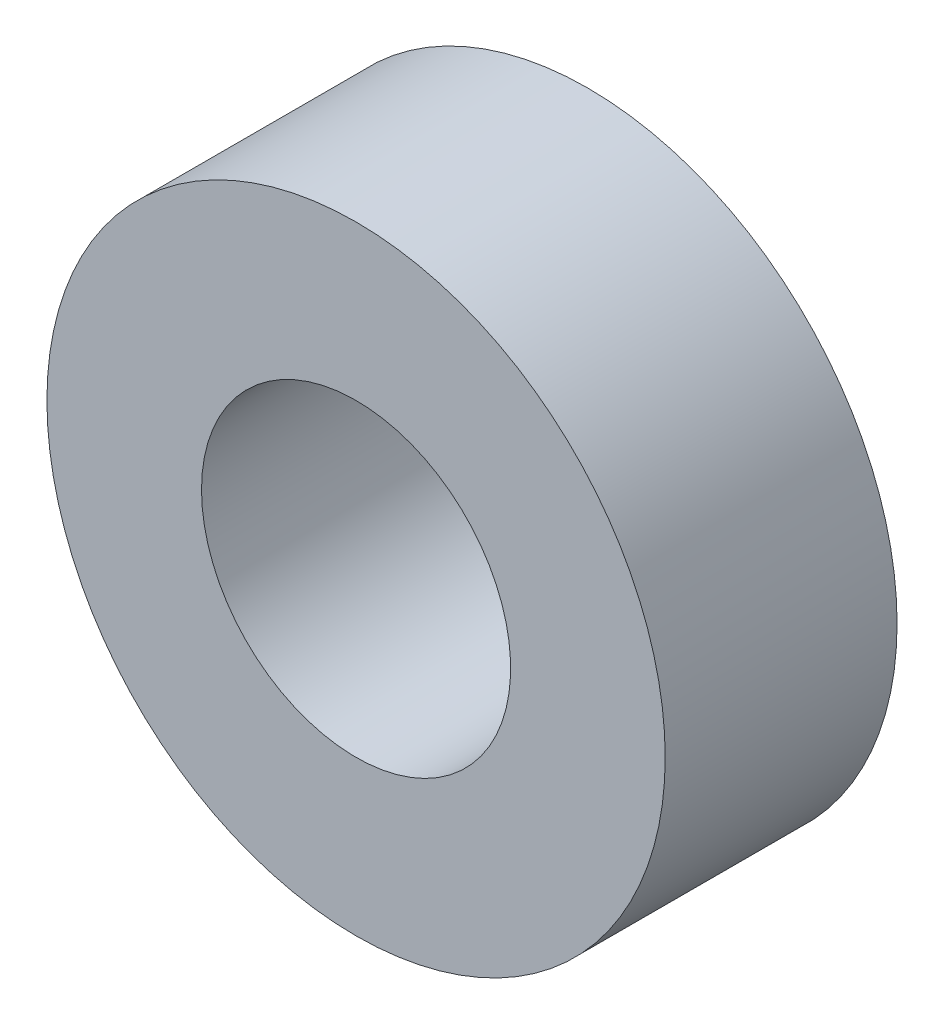
SolidWorks part; units mm, degrees
ref_plane "Front Plane" through (0, 0, 0) normal (0, 0, 1) x (1, 0, 0)
ref_plane "Top Plane" through (0, 0, 0) normal (0, 1, 0) x (1, 0, 0)
ref_plane "Right Plane" through (0, 0, 0) normal (1, 0, 0) x (0, 0, -1)
sketch "Sketch1" plane through (0, 0, 0) normal (0, 0, 1) x (1, 0, 0)
  circle A0 centre (0, 0) radius 6.35
extrude "Extrude1" add sketch "Sketch1" along normal blind 4.7625
sketch "Sketch2" plane through (0, 0, 0) normal (0, 0, -1) x (-1, 0, 0)
  circle A0 centre (0, 0) radius 3.175
extrude "Extrude2" cut sketch "Sketch2" against normal through all
